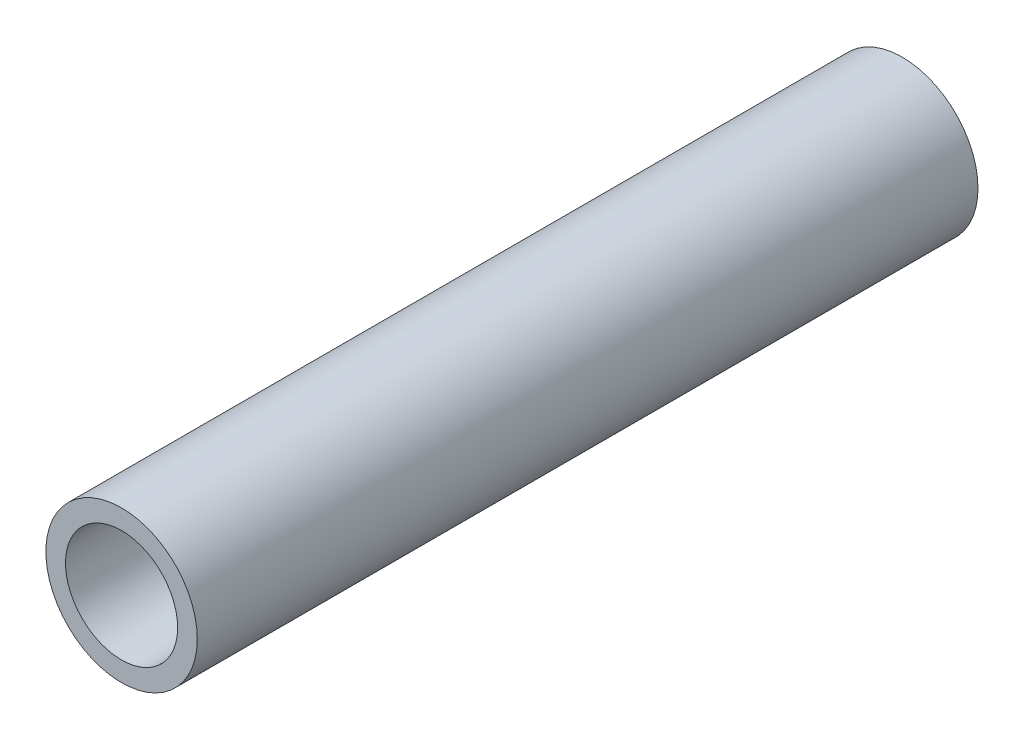
SolidWorks part; units mm, degrees
ref_plane "Front Plane" through (0, 0, 0) normal (0, 0, 1) x (1, 0, 0)
ref_plane "Top Plane" through (0, 0, 0) normal (0, 1, 0) x (1, 0, 0)
ref_plane "Right Plane" through (0, 0, 0) normal (1, 0, 0) x (0, 0, -1)
sketch "Sketch1" plane through (0, 0, 0) normal (0, 0, 1) x (1, 0, 0)
  circle A0 centre (0, 0) radius 10.668
  dimension "Pipe OD" = 21.336
extrude "Extrude-Thin1" add sketch "Sketch1" along normal mid plane 110 thin thin type one direction reverse wall 2.7686
